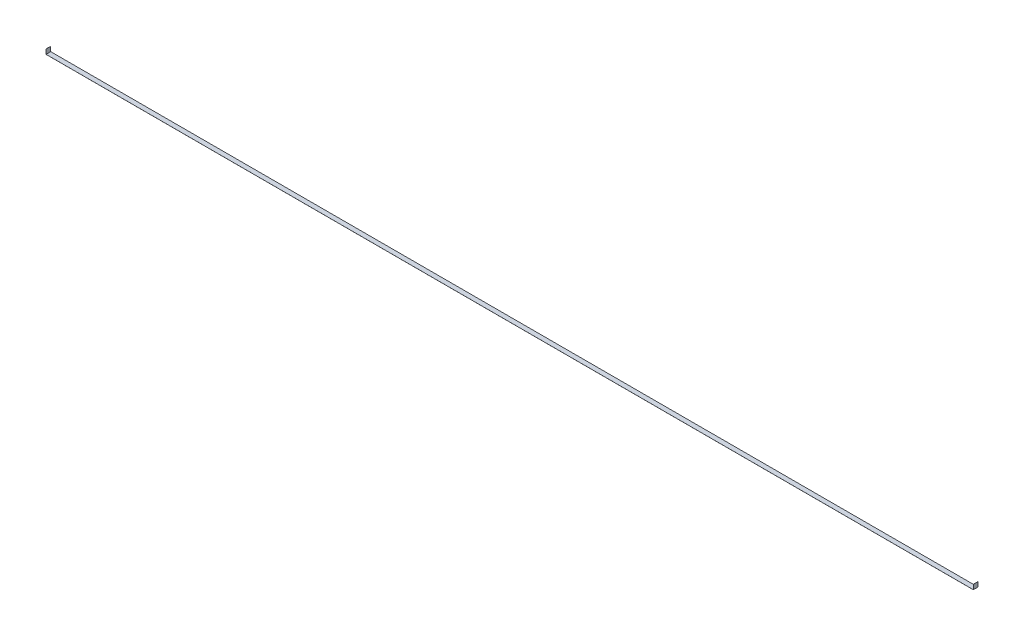
SolidWorks part; units mm, degrees
material "Nylon 101"
ref_plane "Front Plane" through (0, 0, 0) normal (0, 0, 1) x (1, 0, 0)
ref_plane "Top Plane" through (0, 0, 0) normal (0, 1, 0) x (1, 0, 0)
ref_plane "Right Plane" through (0, 0, 0) normal (1, 0, 0) x (0, 0, -1)
sketch "Sketch1" plane through (0, 0, 0) normal (0, 0, 1) x (1, 0, 0)
  line L0 (-2527.3, 0) -> (2527.3, 0)
  line L1 (2527.3, 0) -> (2527.3, 25.4)
  line L2 (-2527.3, 0) -> (-2527.3, 25.4)
  point P4 (0, 0)
  dimension "D1" = 25.4
  dimension "D2" = 5054.6
extrude "Extrude-Thin1" add sketch "Sketch1" along normal mid plane 25.4 thin
